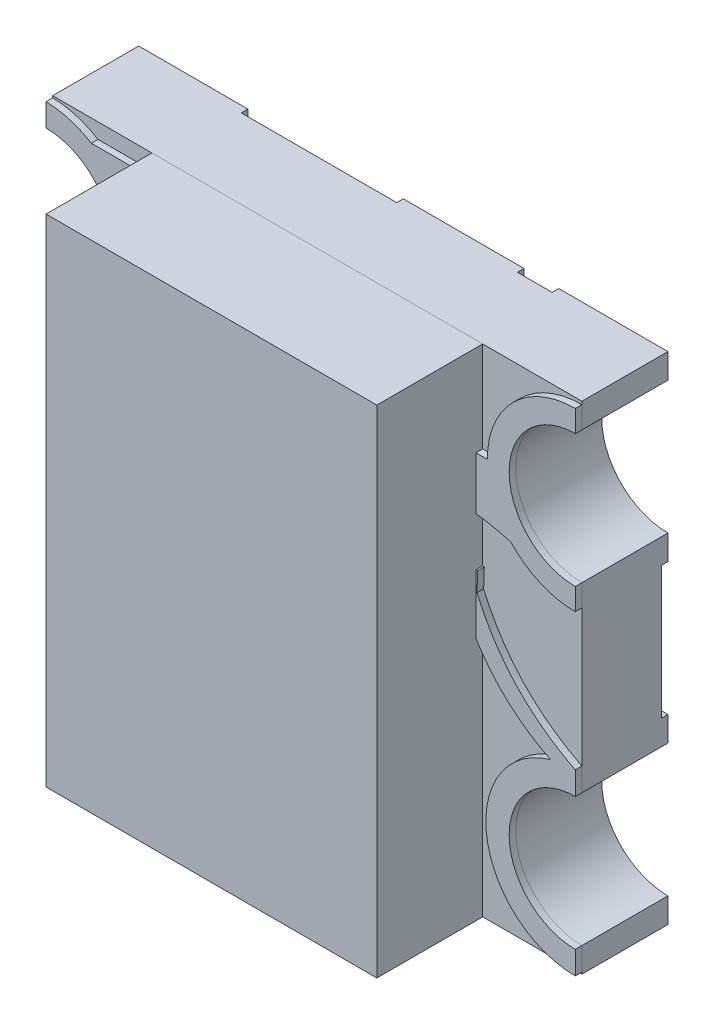
SolidWorks part; units mm, degrees
ref_plane "Front Plane" through (0, 0, 0) normal (0, 0, 1) x (1, 0, 0)
ref_plane "Top Plane" through (0, 0, 0) normal (0, 1, 0) x (1, 0, 0)
ref_plane "Right Plane" through (0, 0, 0) normal (1, 0, 0) x (0, 0, -1)
ref_plane "Plane1" through (0, 0, 0.02) normal (0, 0, -1) x (-1, 0, 0)
sketch "Sketch2" plane through (0, 0, 0.02) normal (0, 0, -1) x (-1, 0, 0)
  line L0 (0, 0.75) -> (0, -0.75) construction
  line L1 (0.8, -0.75) -> (-0.8, -0.75)
  line L2 (0.8, -0.75) -> (0.8, -0.675)
  line L3 (0.8, 0.75) -> (-0.8, 0.75)
  line L4 (-0.8, -0.75) -> (-0.8, -0.675)
  line L5 (0.8, -0.75) -> (-0.8, 0.75) construction
  line L6 (0.8, 0.75) -> (-0.8, -0.75) construction
  line L7 (-0.8, 0) -> (0.8, 0) construction
  line L8 (-0.8, 0.675) -> (-0.8, 0.75)
  line L9 (-0.8, -0.275) -> (-0.8, 0.275)
  line L10 (0.8, 0.675) -> (0.8, 0.75)
  line L11 (0.8, -0.275) -> (0.8, 0.275)
  arc A0 (-0.8, 0.275) -> (-0.8, 0.675) centre (-0.8, 0.475) ccw
  arc A1 (0.8, 0.275) -> (0.8, 0.675) centre (0.8, 0.475) cw
  arc A2 (0.8, -0.275) -> (0.8, -0.675) centre (0.8, -0.475) ccw
  arc A3 (-0.8, -0.275) -> (-0.8, -0.675) centre (-0.8, -0.475) cw
  point P0 (0, 0)
  dimension "0.25" = 0.2
  dimension "D1" = 1.6
  dimension "D2" = 1.5
  dimension "D3" = 0.275
  dimension "D5" = 0.275
extrude "Boss-Extrude1" add sketch "Sketch2" against normal blind 0.24
sketch "Sketch3" plane through (0, 0, 0.02) normal (0, 0, -1) x (-1, 0, 0)
  line L0 (-0.8, 0.275) -> (-0.8, 0.2)
  line L1 (-0.8, 0.2) -> (-0.47, 0.2)
  line L3 (-0.8, 0.75) -> (-0.47, 0.75)
  line L4 (-0.47, 0.2) -> (-0.47, 0.75)
  line L5 (-0.8, 0.2) -> (-0.47, 0.75) construction
  line L6 (-0.8, 0.75) -> (-0.47, 0.2) construction
  line L7 (0, 0) -> (-0.8, 0) construction
  line L8 (-0.8, 0.275) -> (-0.8, -0.275) construction
  line L9 (0.8, 0.75) -> (-0.8, 0.75) construction
  line L10 (0.47, 0.2) -> (0.47, 0.75)
  line L11 (0.8, 0.2) -> (0.47, 0.2)
  line L12 (0.8, 0.275) -> (0.8, 0.2)
  line L13 (0.8, 0.675) -> (0.8, 0.75)
  line L14 (0.8, 0.75) -> (0.47, 0.75)
  line L15 (0, 0) -> (0, 0.75) construction
  line L16 (-0.8, 0.675) -> (-0.8, 0.75)
  line L17 (-0.8, -0.75) -> (-0.47, -0.2) construction
  line L18 (-0.8, -0.2) -> (-0.47, -0.75) construction
  line L19 (-0.8, -0.675) -> (-0.8, -0.75)
  line L20 (0.8, -0.75) -> (0.47, -0.75)
  line L21 (0.8, -0.675) -> (0.8, -0.75)
  line L22 (0.8, -0.275) -> (0.8, -0.2)
  line L23 (0.8, -0.2) -> (0.47, -0.2)
  line L24 (0.47, -0.2) -> (0.47, -0.75)
  line L25 (-0.47, -0.2) -> (-0.47, -0.75)
  line L26 (-0.8, -0.75) -> (-0.47, -0.75)
  line L28 (-0.8, -0.2) -> (-0.47, -0.2)
  line L29 (-0.8, -0.275) -> (-0.8, -0.2)
  line L30 (-0.8, -0.75) -> (0.8, -0.75) construction
  line L31 (-0.3649, -0.75) -> (0, -0.75)
  line L32 (-0.3649, -0.75) -> (-0.3649, 0.75)
  line L33 (-0.3649, 0.75) -> (0, 0.75)
  line L34 (0, -0.75) -> (0, 0.75)
  arc A0 (0.8, 0.275) -> (0.8, 0.675) centre (0.8, 0.475) cw
  arc A1 (-0.8, -0.275) -> (-0.8, -0.675) centre (-0.8, -0.475) cw
  arc A2 (-0.8, 0.275) -> (-0.8, 0.675) centre (-0.8, 0.475) ccw
  arc A3 (-0.8, 0.275) -> (-0.8, 0.675) centre (-0.8, 0.475) ccw
  arc A4 (0.8, -0.275) -> (0.8, -0.675) centre (0.8, -0.475) ccw
  point P0 (-0.635, 0.475)
  point P39 (-0.635, -0.475)
  line M6 (-0.8, 0.75) -> (-0.8, 0.675)
  arc M7 (-0.8, 0.675) -> (-0.8, 0.275) centre (-0.8, 0.475) cw
  line M8 (-0.8, 0.275) -> (-0.8, -0.275)
  arc M9 (-0.8, -0.275) -> (-0.8, -0.675) centre (-0.8, -0.475) cw
  line M10 (-0.8, -0.675) -> (-0.8, -0.75)
  line M11 (-0.8, -0.75) -> (0.8, -0.75)
  line M12 (0.8, -0.75) -> (0.8, -0.675)
  arc M13 (0.8, -0.675) -> (0.8, -0.275) centre (0.8, -0.475) cw
  line M14 (0.8, -0.275) -> (0.8, 0.275)
  arc M15 (0.8, 0.275) -> (0.8, 0.675) centre (0.8, 0.475) cw
  line M16 (0.8, 0.675) -> (0.8, 0.75)
  line M17 (0.8, 0.75) -> (-0.8, 0.75)
  dimension "D1" = 0.33
  dimension "D2" = 0.2
  dimension "D4" = 0.55
  dimension "D5" = 0
extrude "Boss-Extrude2" add sketch "Sketch3" along normal blind 0.02 contours L1 L4 L3 M6 M7 M8 | L14 L10 L11 M16 M14 M15 | L23 L24 L20 M12 M13 M14 | L28 L26 L25 M8 M9 M10 | L34 L32 M11 M17
sketch "Sketch4" plane through (0, 0, 0.26) normal (0, 0, 1) x (1, 0, 0)
  line L0 (71.5675, 201.9477) -> (362.2342, 201.9477) construction
  line L1 (0.8, -0.675) -> (0.8, -0.75) construction
  line L2 (0.8, 0.275) -> (0.8, -0.275) construction
  line L3 (-0.4415, 0.5687) -> (0.2679, 0.5687)
  line L4 (0.2679, 0.5687) -> (0.2679, 0.7039)
  line L5 (0.2679, 0.7039) -> (-0.6632, 0.7039)
  line L6 (0.8, -0.2053) -> (0.8, -0.275)
  line L7 (-0.8, -0.275) -> (-0.8, 0.275) construction
  line L8 (0.8, -0.675) -> (0.8, -0.7447)
  line L9 (-0.4415, 0.5687) -> (-0.5526, 0.5687)
  line L10 (0.3812, 0.1728) -> (0.3753, 0)
  line L11 (-0.8, 0.675) -> (-0.8, 0.7443)
  line L12 (-0.8, 0.275) -> (-0.8, 0.2057)
  line L13 (0.3753, 0) -> (0.4952, -0.0042)
  line L14 (0.3812, 0.1728) -> (0.5048, 0.1685)
  line L15 (0.5048, 0.1685) -> (0.5028, 0.11)
  line L16 (-0.8, -0.75) -> (-0.8, -0.675) construction
  line L17 (-0.8, -0.2075) -> (-0.8, -0.275)
  line L18 (-0.8, -0.675) -> (-0.8, -0.7425)
  line L19 (-0.4649, -0.1065) -> (0.3651, -0.1208)
  line L20 (0.3651, -0.1208) -> (0.3575, -0.5641)
  line L21 (0.3575, -0.5641) -> (-0.4649, -0.55)
  line L22 (-0.4649, -0.1065) -> (-0.471, -0.4649)
  line L23 (0.8, 0.75) -> (0.8, 0.675) construction
  line L24 (0.8, 0.741) -> (0.8, 0.675)
  line L25 (0.8, 0.275) -> (0.8, 0.209)
  line L26 (0.2679, 0.0135) -> (0.2679, 0.3188)
  line L27 (0.2679, 0.0135) -> (-0.4649, 0.0135)
  line L28 (-0.4649, 0.0135) -> (-0.4649, 0.475)
  line L29 (71.8228, 202.5556) -> (362.4895, 202.5556) construction
  line L30 (-0.4649, 0.475) -> (0.534, 0.475)
  arc A0 (-0.8, 0.7443) -> (-0.6632, 0.7039) centre (-0.8051, 0.475) cw
  arc A1 (-0.8, 0.675) -> (-0.8, 0.275) centre (-0.8, 0.475) cw
  arc A2 (-0.8, 0.275) -> (-0.8, 0.675) centre (-0.8, 0.475) ccw construction
  arc A3 (-0.5526, 0.5687) -> (-0.8, 0.2057) centre (-0.8051, 0.475) cw
  arc A4 (0.8, -0.7447) -> (0.7248, -0.2157) centre (0.7993, -0.475) cw
  arc A5 (0.7022, -0.3006) -> (0.8, -0.675) centre (0.8, -0.475) ccw
  arc A6 (0.8, -0.275) -> (0.8, -0.675) centre (0.8, -0.475) ccw construction
  arc A7 (0.8, 0.675) -> (0.8, 0.275) centre (0.8, 0.475) ccw
  arc A8 (-0.8, -0.275) -> (-0.8, -0.675) centre (-0.8, -0.475) cw
  arc A9 (-0.8, -0.675) -> (-0.8, -0.275) centre (-0.8, -0.475) ccw construction
  arc A10 (0.8, 0.675) -> (0.8, 0.275) centre (0.8, 0.475) ccw construction
  arc A11 (-0.8, -0.7425) -> (-0.5526, -0.5767) centre (-0.8, -0.475) ccw
  arc A12 (-0.5361, -0.5186) -> (-0.8, -0.2075) centre (-0.8, -0.475) ccw
  arc A13 (0.8, 0.741) -> (0.534, 0.475) centre (0.8, 0.475) ccw
  arc A14 (0.605, 0.294) -> (0.8, 0.209) centre (0.8, 0.475) ccw
  spline S0 degree 2 poles (0.4952, -0.0042) (0.5776, -0.1425) (0.7248, -0.2157) knots 0 0 0 1 1 1
  spline S1 degree 2 poles (0.5028, 0.11) (0.5944, -0.1016) (0.8, -0.2053) knots 0 0 0 1 1 1
  spline S2 degree 2 poles (-0.471, -0.4649) (-0.5083, -0.4857) (-0.5361, -0.5186) knots 0 0 0 1 1 1
  spline S3 degree 2 poles (-0.4649, -0.55) (-0.5135, -0.5418) (-0.5526, -0.5767) knots 0 0 0 1 1 1
  spline S4 degree 2 poles (0.2679, 0.3188) (0.4364, 0.3399) (0.605, 0.294) knots 0 0 0 1 1 1
extrude "Boss-Extrude3" add sketch "Sketch4" along normal blind 0.02 separate body
sketch "Sketch5" plane through (0, 0, 0.26) normal (0, 0, 1) x (1, 0, 0)
  line L1 (-0.4343, 0.3938) -> (0.214, 0.3938)
  line L2 (-0.4343, 0.3938) -> (-0.4343, 0.0552)
  line L3 (-0.4343, 0.0552) -> (0.214, 0.0552)
  line L4 (0.214, 0.3938) -> (0.214, 0.0552)
  line L5 (-0.1178, -0.3594) -> (0.0558, -0.3594)
  line L6 (-0.1178, -0.3594) -> (-0.1178, -0.5316)
  line L7 (-0.1178, -0.5316) -> (0.0558, -0.5316)
  line L8 (0.0558, -0.3594) -> (0.0558, -0.5316)
  line L9 (-0.4135, -0.3594) -> (-0.3096, -0.3594)
  line L10 (-0.4135, -0.3594) -> (-0.4135, -0.5316)
  line L11 (-0.4135, -0.5316) -> (-0.3096, -0.5316)
  line L12 (-0.3096, -0.3594) -> (-0.3096, -0.5316)
  line L13 (0.2532, -0.3594) -> (0.3433, -0.3594)
  line L14 (0.2532, -0.3594) -> (0.2532, -0.5316)
  line L15 (0.2532, -0.5316) -> (0.3433, -0.5316)
  line L16 (0.3433, -0.3594) -> (0.3433, -0.5316)
  point P16 (0.2207, 0.0552)
  point P17 (0.214, 0.3938)
extrude "Boss-Extrude4" add sketch "Sketch5" along normal blind 0.021 separate body
sketch "Sketch6" plane through (0, 0, 0.26) normal (0, 0, 1) x (1, 0, 0)
  line L0 (-0.8, 0.75) -> (0.8, 0.75) construction
  line L1 (0.5, -0.75) -> (-0.5, -0.75)
  line L2 (0.5, -0.75) -> (0.5, 0.75)
  line L3 (0.5, 0.75) -> (-0.5, 0.75)
  line L4 (-0.5, -0.75) -> (-0.5, 0.75)
  line L5 (0.5, -0.75) -> (-0.5, 0.75) construction
  line L6 (0.5, 0.75) -> (-0.5, -0.75) construction
  point P0 (0, 0)
  dimension "D1" = 1
extrude "Boss-Extrude5" add sketch "Sketch6" along normal blind 0.32 separate body
